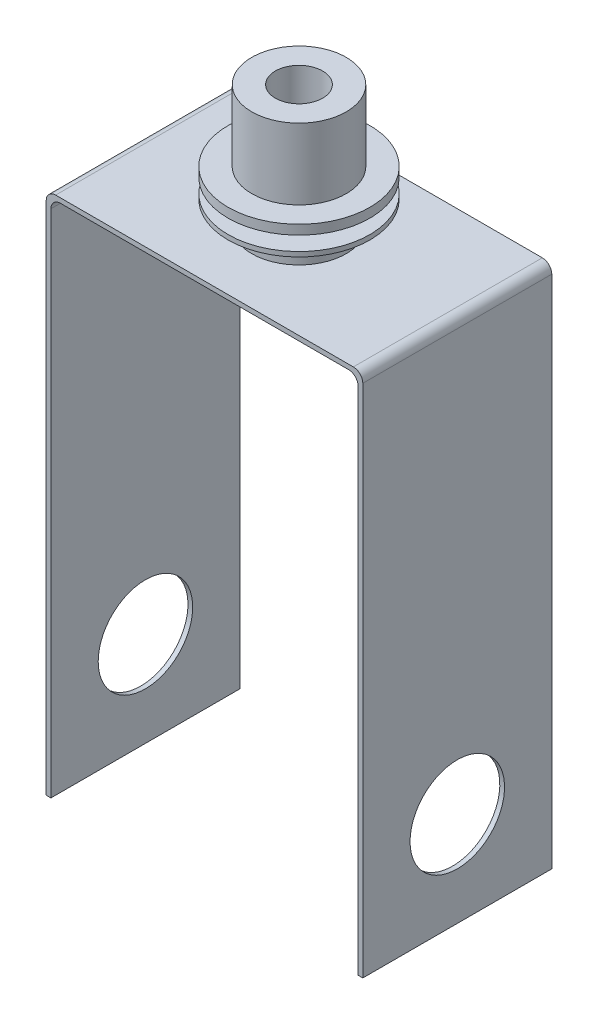
SolidWorks part; units mm, degrees
material "PE High Density"
ref_plane "Front Plane" through (0, 0, 0) normal (0, 0, 1) x (1, 0, 0)
ref_plane "Top Plane" through (0, 0, 0) normal (0, 1, 0) x (1, 0, 0)
ref_plane "Right Plane" through (0, 0, 0) normal (1, 0, 0) x (0, 0, -1)
sketch "Sketch1" plane through (0, 0, 0) normal (0, 0, 1) x (1, 0, 0)
  line L0 (42.545, 113.03) -> (42.545, -25.4)
  line L1 (-38.735, 114.3) -> (38.735, 114.3)
  line L2 (-41.275, 111.76) -> (-41.275, -25.4)
  line L4 (41.275, 111.76) -> (41.275, -25.4)
  line L5 (-41.275, 114.3) -> (41.275, -25.4) construction
  line L6 (-41.275, -25.4) -> (41.275, 114.3) construction
  line L7 (-40.005, 115.57) -> (40.005, 115.57)
  line L8 (-42.545, 113.03) -> (-42.545, -25.4)
  line L9 (-42.545, -25.4) -> (-41.275, -25.4)
  line L10 (41.275, -25.4) -> (42.545, -25.4)
  line L11 (41.275, 114.3) -> (41.275, -25.4) construction
  line L12 (-41.275, 114.3) -> (41.275, 114.3) construction
  line L13 (42.545, 115.57) -> (42.545, -25.4) construction
  line L14 (-42.545, 115.57) -> (42.545, 115.57) construction
  line L15 (-42.545, 115.57) -> (-42.545, -25.4) construction
  line L16 (-41.275, 114.3) -> (-41.275, -25.4) construction
  arc A0 (41.275, 111.76) -> (38.735, 114.3) centre (38.735, 111.76) ccw
  arc A1 (42.545, 113.03) -> (40.005, 115.57) centre (40.005, 113.03) ccw
  arc A2 (-42.545, 113.03) -> (-40.005, 115.57) centre (-40.005, 113.03) cw
  arc A3 (-41.275, 111.76) -> (-38.735, 114.3) centre (-38.735, 111.76) cw
  point P0 (0, 44.45)
  dimension "D6" = 2.54
  dimension "D1" = 82.55
  dimension "D2" = 1.27
  dimension "D3" = 139.7
  dimension "D4" = 82.55
  dimension "D5" = 114.3
extrude "Boss-Extrude1" add sketch "Sketch1" along normal blind 50.8 contours L8 L9 L2 A3 L1 A0 L4 L10 L0 A1 L7 A2
sketch "Sketch2" plane through (-42.545, 0, 0) normal (-1, 0, 0) x (0, 0, 1)
  line L1 (50.8, -25.4) -> (0, -25.4) construction
  circle A0 centre (25.4, 0) radius 12.7
  point P6 (25.4, -25.4)
  dimension "D1" = 25.4
  dimension "D2" = 25.4
extrude "Cut-Extrude1" cut sketch "Sketch2" against normal through all
sketch "Sketch3" plane through (0, 115.57, 0) normal (0, 1, 0) x (1, 0, 0)
  line L0 (-42.545, -50.8) -> (-42.545, 0) construction
  circle A0 centre (0, -25.4) radius 12.7
  point P4 (-42.545, -25.4)
  dimension "D1" = 25.4
extrude "Boss-Extrude2" add sketch "Sketch3" along normal blind 6.35 contours A0
sketch "Sketch4" plane through (0, 121.92, 0) normal (0, 1, 0) x (1, 0, 0)
  circle A0 centre (0, -25.4) radius 19.05
  dimension "D1" = 38.1
extrude "Boss-Extrude3" add sketch "Sketch4" along normal blind 1.27
sketch "Sketch5" plane through (0, 123.19, 0) normal (0, 1, 0) x (1, 0, 0)
  circle A0 centre (0, -25.4) radius 12.7
  dimension "D1" = 25.4
extrude "Boss-Extrude4" add sketch "Sketch5" along normal blind 25.4 contours A0
sketch "Sketch6" plane through (0, 148.59, 0) normal (0, 1, 0) x (1, 0, 0)
  circle A0 centre (0, -25.4) radius 6.35
  dimension "D1" = 12.7
extrude "Cut-Extrude2" cut sketch "Sketch6" against normal through all
ref_plane "Plane1" through (0, 127, 0) normal (0, 1, 0) x (1, 0, 0)
sketch "Sketch7" plane through (0, 127, 0) normal (0, 1, 0) x (1, 0, 0)
  circle A0 centre (0, -25.4) radius 12.7
  circle A1 centre (0, -25.4) radius 19.05
  dimension "D1" = 38.1
  dimension "D2" = 25.4
extrude "Boss-Extrude5" add sketch "Sketch7" along normal blind 2.54
